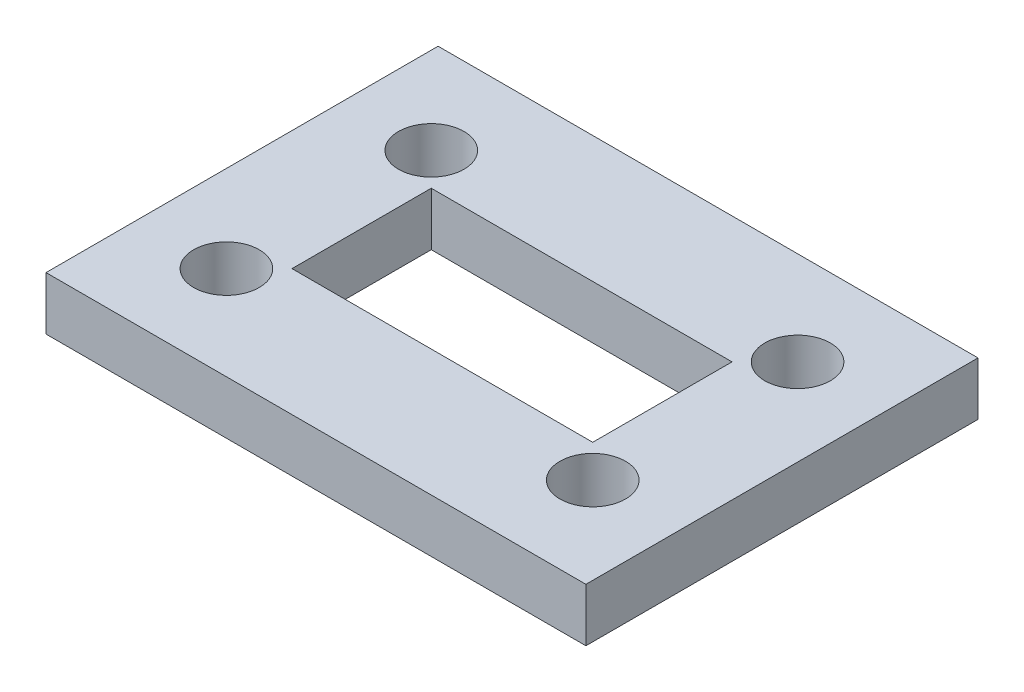
SolidWorks part; units mm, degrees
ref_plane "Front Plane" through (0, 0, 0) normal (0, 0, 1) x (1, 0, 0)
ref_plane "Top Plane" through (0, 0, 0) normal (0, 1, 0) x (1, 0, 0)
ref_plane "Right Plane" through (0, 0, 0) normal (1, 0, 0) x (0, 0, -1)
sketch "Sketch1" plane through (0, 0, 0) normal (0, 1, 0) x (1, 0, 0)
  line L0 (-111.76, 0) -> (-111.76, 9.42)
  line L1 (0, 0) -> (-111.76, 0)
  line L2 (0, 0) -> (0, 75.69)
  line L3 (0, 75.69) -> (-111.76, 75.69)
  line L4 (-111.76, 0) -> (-111.76, 9.42)
  line L5 (-111.76, 9.42) -> (-100.58, 9.42)
  line L7 (-111.76, 16.28) -> (-100.58, 16.28)
  line L8 (-111.76, 16.28) -> (-111.76, 75.69)
  line L9 (0, 0) -> (0, 37.845)
  line L10 (0, 37.845) -> (-111.76, 37.845)
  line L11 (-55.88, 75.69) -> (-55.88, 0)
  line L12 (-111.76, 66.27) -> (-100.58, 66.27)
  line L13 (-111.76, 59.41) -> (-100.58, 59.41)
  line L14 (0, 9.42) -> (-11.18, 9.42)
  line L15 (0, 16.28) -> (-11.18, 16.28)
  line L16 (0, 59.41) -> (-11.18, 59.41)
  line L17 (0, 66.27) -> (-11.18, 66.27)
  arc A0 (-100.58, 9.42) -> (-100.58, 16.28) centre (-100.58, 12.85) ccw
  arc A1 (-100.58, 66.27) -> (-100.58, 59.41) centre (-100.58, 62.84) cw
  arc A2 (-11.18, 9.42) -> (-11.18, 16.28) centre (-11.18, 12.85) cw
  arc A3 (-11.18, 66.27) -> (-11.18, 59.41) centre (-11.18, 62.84) ccw
  dimension "D1" = 111.76
  dimension "D2" = 75.69
sketch "Sketch2" plane through (0, 0, 0) normal (0, 1, 0) x (1, 0, 0)
  line L0 (-55.88, 0) -> (-55.88, 75.69)
  line L1 (-111.76, 0) -> (-121.76, 0)
  line L2 (-111.76, 0) -> (-111.76, -10)
  line L3 (-111.76, -10) -> (-121.76, -10)
  line L4 (-121.76, 0) -> (-121.76, -10)
  line L5 (0, 75.69) -> (10, 75.69)
  line L6 (0, 75.69) -> (0, 85.69)
  line L7 (0, 85.69) -> (10, 85.69)
  line L8 (10, 75.69) -> (10, 85.69)
  line L9 (-111.76, 37.845) -> (0, 37.845)
  circle A0 centre (-100.58, 12.85) radius 3.43
  circle A1 centre (-100.58, 12.85) radius 8
  circle A2 centre (-100.58, 62.84) radius 8
  circle A3 centre (-11.18, 12.85) radius 8
  circle A4 centre (-11.18, 62.84) radius 8
  dimension "D1" = 10
  dimension "D2" = 10
  dimension "D3" = 10
  dimension "D4" = 10
sketch "Sketch3" plane through (0, 0, 0) normal (0, 1, 0) x (1, 0, 0)
  line L0 (-100.58, 54.84) -> (-92.58, 54.84)
  line L1 (-121.76, -10) -> (-108.58, -10)
  line L2 (-121.76, -10) -> (-121.76, 12.85)
  line L5 (-108.58, -10) -> (-11.18, -10)
  line L9 (10, 85.69) -> (-3.18, 85.69)
  line L10 (10, 85.69) -> (10, 62.84)
  line L14 (10, 62.84) -> (10, -10)
  line L15 (10, -10) -> (-3.18, -10)
  line L19 (-11.18, -10) -> (-3.18, -10)
  line L22 (-121.76, 12.85) -> (-121.76, 62.84)
  line L26 (-121.76, 62.84) -> (-121.76, 85.69)
  line L27 (-121.76, 85.69) -> (-108.58, 85.69)
  line L29 (-108.58, 85.69) -> (-11.18, 85.69)
  line L35 (-11.18, 85.69) -> (-3.18, 85.69)
  line L37 (-92.58, 62.84) -> (-92.58, 54.84)
  line L38 (-19.18, 12.85) -> (-19.18, 20.85)
  line L39 (-11.18, 20.85) -> (-19.18, 20.85)
  line L41 (-92.58, 54.84) -> (-19.18, 54.84)
  line L42 (-92.58, 54.84) -> (-92.58, 20.85)
  line L43 (-92.58, 20.85) -> (-19.18, 20.85)
  line L44 (-19.18, 54.84) -> (-19.18, 20.85)
  circle A1 centre (-11.18, 12.85) radius 8 construction
  circle A3 centre (-100.58, 62.84) radius 8 construction
  circle A4 centre (-100.58, 62.84) radius 8
  circle A5 centre (-11.18, 62.84) radius 8
  circle A6 centre (-11.18, 12.85) radius 8
  circle A7 centre (-100.58, 12.85) radius 8
extrude "Boss-Extrude1" add sketch "Sketch3" along normal blind 13 contours L35 L29 L27 L26 L22 L2 L1 L5 L19 L15 L14 L10 L9 A7 A6 L38 L43 L42 L0 A4 L37 L41 L44 L39 A5 | A4 L0 L37 | A6 L39 L38
